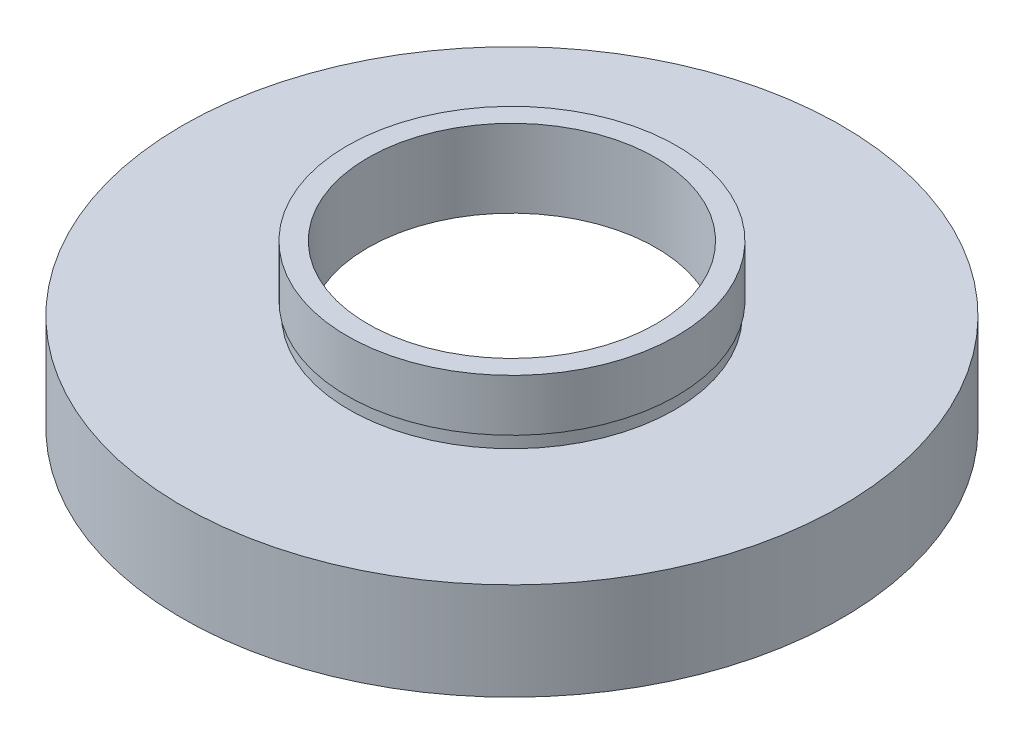
SolidWorks part; units mm, degrees
ref_plane "前视基准面" through (0, 0, 0) normal (0, 0, 1) x (1, 0, 0)
ref_plane "上视基准面" through (0, 0, 0) normal (0, 1, 0) x (1, 0, 0)
ref_plane "右视基准面" through (0, 0, 0) normal (1, 0, 0) x (0, 0, -1)
sketch "草图1" plane through (0, 0, 0) normal (0, 0, 1) x (1, 0, 0)
  line L0 (0, 16.886) -> (0, -24.4878) construction
  line L1 (23.5, 0) -> (23.5, 5.5)
  line L2 (11.1, 6.5) -> (24.1, 6.5)
  line L3 (11.1, 6.5) -> (11.1, 12.5)
  line L4 (11.1, 12.5) -> (12.7, 12.5)
  line L5 (12.7, 12.5) -> (12.7, 8.5)
  line L6 (12.7, 8.5) -> (12.55, 8.5)
  line L7 (12.55, 8.5) -> (12.55, 7.5)
  line L8 (12.55, 7.5) -> (25.4, 7.5)
  line L9 (25.4, 7.5) -> (25.4, 0)
  line L10 (25.4, 0) -> (23.5, 0)
  line L11 (23.5, 5.5) -> (24.1, 5.5)
  line L12 (24.1, 5.5) -> (24.1, 6.5)
  line L13 (0, 0) -> (3.4668, 0) construction
  point P4 (24.45, 0)
  dimension "D1" = 11.1
  dimension "D2" = 12.7
  dimension "D3" = 12.55
  dimension "D4" = 23.5
  dimension "D5" = 24.1
  dimension "D6" = 25.4
  dimension "D7" = 12.5
  dimension "D8" = 7.5
  dimension "D9" = 1
  dimension "D10" = 5.5
  dimension "D11" = 1
revolve "旋转1" add sketch "草图1" angle 360 about L0
cosmetic thread "装饰螺纹线1" parameters "D2"=24.4
cosmetic thread "装饰螺纹线2" parameters "D2"=23.2
cosmetic thread "装饰螺纹线3" parameters "D2"=48
